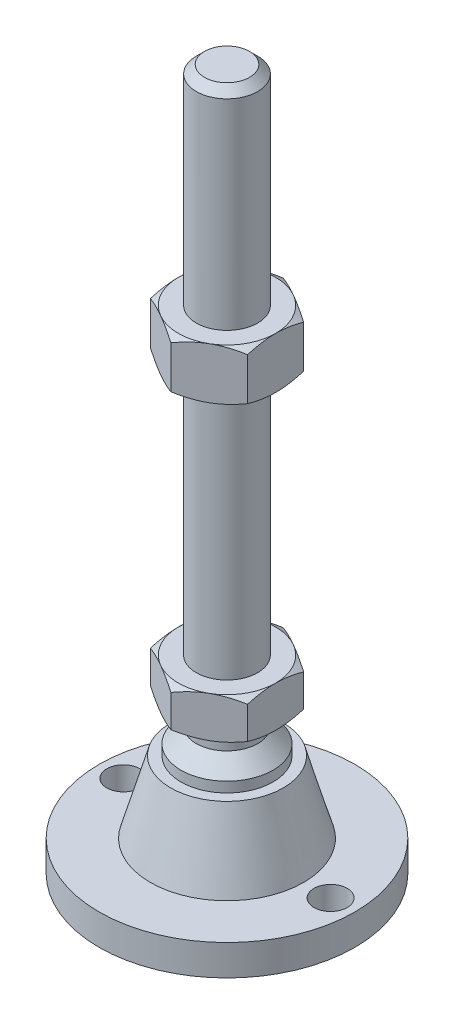
SolidWorks part; units mm, degrees
ref_plane "Спереди" through (0, 0, 0) normal (0, 0, 1) x (1, 0, 0)
ref_plane "Сверху" through (0, 0, 0) normal (0, 1, 0) x (1, 0, 0)
ref_plane "Справа" through (0, 0, 0) normal (1, 0, 0) x (0, 0, -1)
sketch "Эскиз1" plane through (0, 0, 0) normal (0, 0, 1) x (1, 0, 0)
  line L0 (0, 0) -> (-25, 0)
  line L3 (-25, 0) -> (-25, 6)
  line L12 (-6, 37) -> (-6, 135.4)
  line L13 (-6, 135.4) -> (-4.4, 137)
  line L14 (-4.4, 137) -> (0, 137)
  line L15 (0, 137) -> (0, 0) construction
  line L16 (-25, 6) -> (-15, 6)
  line L17 (0, 0) -> (0, 137)
  line L18 (0, 0) -> (0, -7.9595) construction
  line L19 (-6, 37) -> (-6, 29)
  line L21 (-9, 20) -> (-11, 20)
  line L22 (-15, 6) -> (-11, 20)
  line L23 (-9, 20) -> (-9, 22)
  line L24 (-9, 22) -> (-6, 25)
  line L25 (-6, 25) -> (-6, 29)
  line L26 (-6, 37) -> (0, 37) construction
  point P8 (-6, 86.2)
revolve "Повернуть1" add sketch "Эскиз1" angle 360 about L17
ref_plane "Плоскость2" through (0, 29, 0) normal (0, 1, 0) x (1, 0, 0)
sketch "Эскиз2" plane through (0, 29, 0) normal (0, 1, 0) x (1, 0, 0)
  line L1 (0, 10.9697) -> (-9.5, 5.4848)
  line L2 (-9.5, 5.4848) -> (-9.5, -5.4848)
  line L3 (-9.5, -5.4848) -> (0, -10.9697)
  line L4 (0, -10.9697) -> (9.5, -5.4848)
  line L5 (9.5, -5.4848) -> (9.5, 5.4848)
  line L6 (9.5, 5.4848) -> (0, 10.9697)
  circle A0 centre (0, 0) radius 9.5 construction
  dimension "D1" = 19
extrude "Бобышка-Вытянуть1" add sketch "Эскиз2" along normal up to vertex (8 mm away) up to point (-6, 37, 0)
ref_plane "Плоскость1" through (0, 86.2, 0) normal (0, 1, 0) x (1, 0, 0)
sketch "Эскиз3" plane through (0, 86.2, 0) normal (0, 1, 0) x (1, 0, 0)
  line L6 (9.5, 5.4848) -> (0, 10.9697)
  line L7 (0, 10.9697) -> (-9.5, 5.4848)
  line L8 (-9.5, 5.4848) -> (-9.5, -5.4848)
  line L9 (-9.5, -5.4848) -> (0, -10.9697)
  line L10 (0, -10.9697) -> (9.5, -5.4848)
  line L11 (9.5, -5.4848) -> (9.5, 5.4848)
  line L12 (9.5, 5.4848) -> (0, 10.9697)
  line L13 (0, 10.9697) -> (-9.5, 5.4848)
  line L14 (-9.5, 5.4848) -> (-9.5, -5.4848)
  line L15 (-9.5, -5.4848) -> (0, -10.9697)
  line L16 (0, -10.9697) -> (9.5, -5.4848)
  line L17 (9.5, -5.4848) -> (9.5, 5.4848)
  dimension "D1" = 0
extrude "Бобышка-Вытянуть2" add sketch "Эскиз3" along normal blind 10
sketch "Эскиз4" plane through (0, 0, 0) normal (0, 0, 1) x (1, 0, 0)
  line L0 (-9.5, 96.2) -> (-18.1603, 91.2)
  line L1 (-18.1603, 91.2) -> (-18.1603, 96.2)
  line L2 (-18.1603, 96.2) -> (-9.5, 96.2)
  line L3 (-18.1603, 91.2) -> (-9.5, 86.2)
  line L4 (50, 86.2) -> (-50, 86.2) construction
  line L5 (-9.5, 86.2) -> (-18.1603, 86.2)
  line L6 (-18.1603, 86.2) -> (-18.1603, 91.2)
  line L7 (-9.5, 96.2) -> (-9.5, 86.2) construction
  line L8 (-9.5, 37) -> (-16.4282, 37)
  line L9 (-16.4282, 37) -> (-16.4282, 33)
  line L10 (-16.4282, 33) -> (-9.5, 37)
  line L11 (-9.5, 29) -> (-16.4282, 33)
  line L12 (-16.4282, 33) -> (-16.4282, 29)
  line L13 (-16.4282, 29) -> (-9.5, 29)
  line L14 (0, 137) -> (0, 96.3793) construction
  line L15 (50, 29) -> (-50, 29) construction
  dimension "D1" = 30
  dimension "D2" = 30
revolve "Вырез-Повернуть2" cut sketch "Эскиз4" angle 360 about L14
sketch "Эскиз5" plane through (0, 6, 0) normal (0, 1, 0) x (1, 0, 0)
  line L0 (20.25, 0) -> (-20.25, 0) construction
  circle A0 centre (-20.25, 0) radius 3.25
  circle A1 centre (20.25, 0) radius 3.25
  circle A2 centre (0, 0) radius 25 construction
  dimension "D1" = 6.5
  dimension "D2" = 1.5
extrude "Вырез-Вытянуть1" cut sketch "Эскиз5" against normal through all
equation "\"D13@Эскиз1\"=\"D12@Эскиз1\"/2"
